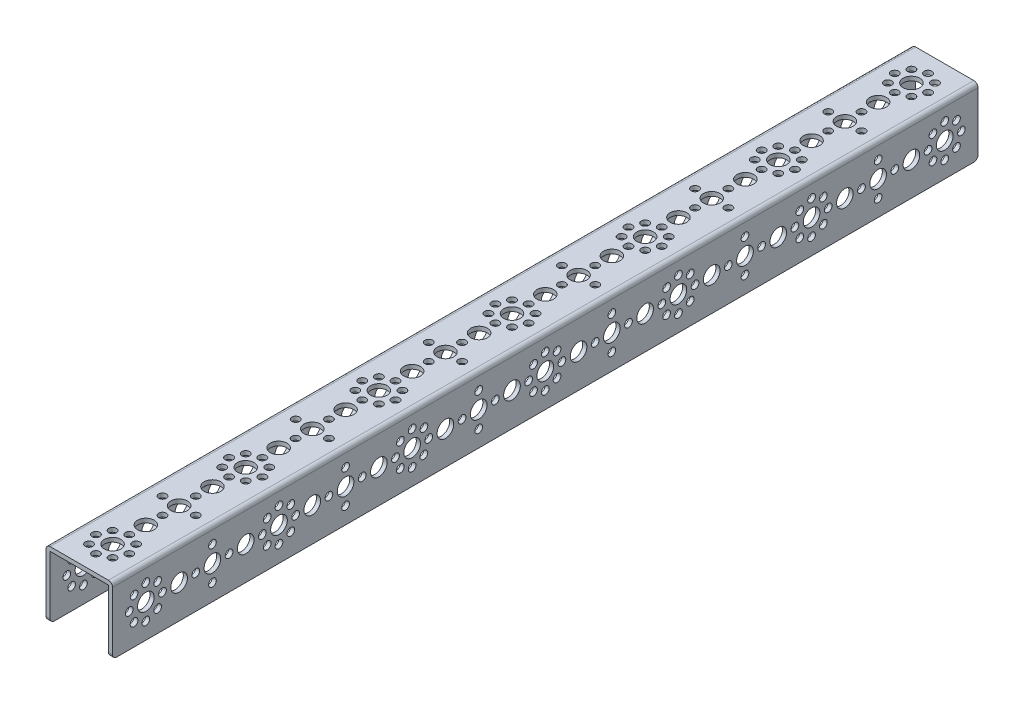
SolidWorks part; units mm, degrees
ref_plane "Front Plane" through (0, 0, 0) normal (0, 0, 1) x (1, 0, 0)
ref_plane "Top Plane" through (0, 0, 0) normal (0, 1, 0) x (1, 0, 0)
ref_plane "Right Plane" through (0, 0, 0) normal (1, 0, 0) x (0, 0, -1)
sketch "Sketch1" plane through (0, 0, 0) normal (0, 0, 1) x (1, 0, 0)
  line L0 (14, -16) -> (16, -16)
  line L1 (-16, 16) -> (16, 16)
  line L2 (-16, 16) -> (-16, -16)
  line L3 (-16, -16) -> (-14, -16)
  line L4 (16, 16) -> (16, -16)
  line L5 (-16, 16) -> (16, -16) construction
  line L6 (-16, -16) -> (16, 16) construction
  line L7 (-14, 14) -> (14, 14)
  line L8 (-14, 14) -> (-14, -16)
  line L10 (14, 14) -> (14, -16)
  point P0 (0, 0)
  dimension "D1" = 32
  dimension "D2" = 32
  dimension "D3" = 2
  dimension "D4" = 2
extrude "Boss-Extrude1" add sketch "Sketch1" against normal blind 416
sketch "Sketch2" plane through (0, 16, 0) normal (0, 1, 0) x (1, 0, 0)
  line L0 (0, 0) -> (0, 307.3895) construction
  line L1 (16, 0) -> (-16, 0) construction
  line L2 (-28.6598, 208) -> (46.6801, 208) construction
  circle B0 centre (0, 256) radius 4
  circle B1 centre (0, 224) radius 4
  circle B2 centre (0.1754, 192) radius 4
  circle B3 centre (0, 160) radius 4
  circle B4 centre (0, 240) radius 4
  circle B5 centre (0, 232) radius 1.85
  circle B6 centre (0, 248) radius 1.85
  circle B7 centre (-8, 240) radius 1.85
  circle B8 centre (8, 240) radius 1.85
  circle B9 centre (0, 264) radius 1.85
  circle B10 centre (-8, 272) radius 1.85
  circle B11 centre (0, 272) radius 4
  circle B12 centre (8, 272) radius 1.85
  circle B13 centre (5.66, 277.66) radius 1.85
  circle B14 centre (-5.66, 277.66) radius 1.85
  circle B15 centre (0, 280) radius 1.85
  circle B16 centre (5.66, 266.34) radius 1.85
  circle B17 centre (-5.66, 266.34) radius 1.85
  circle B18 centre (0, 176) radius 4
  circle B19 centre (0, 168) radius 1.85
  circle B20 centre (0, 184) radius 1.85
  circle B21 centre (-8, 176) radius 1.85
  circle B22 centre (8, 176) radius 1.85
  circle B23 centre (0, 200) radius 1.85
  circle B24 centre (-8, 208) radius 1.85
  circle B25 centre (0, 208) radius 4
  circle B26 centre (8, 208) radius 1.85
  circle B27 centre (5.66, 213.66) radius 1.85
  circle B28 centre (-5.66, 213.66) radius 1.85
  circle B29 centre (0, 216) radius 1.85
  circle B30 centre (5.66, 202.34) radius 1.85
  circle B31 centre (-5.66, 202.34) radius 1.85
  circle B32 centre (0, 32) radius 4
  circle B33 centre (0, 64) radius 4
  circle B34 centre (-0.1754, 96) radius 4
  circle B35 centre (0, 128) radius 4
  circle B36 centre (0, 48) radius 4
  circle B37 centre (0, 56) radius 1.85
  circle B38 centre (0, 40) radius 1.85
  circle B39 centre (8, 48) radius 1.85
  circle B40 centre (-8, 48) radius 1.85
  circle B41 centre (0, 24) radius 1.85
  circle B42 centre (8, 16) radius 1.85
  circle B43 centre (0, 16) radius 4
  circle B44 centre (-8, 16) radius 1.85
  circle B45 centre (-5.66, 10.34) radius 1.85
  circle B46 centre (5.66, 10.34) radius 1.85
  circle B47 centre (0, 8) radius 1.85
  circle B48 centre (-5.66, 21.66) radius 1.85
  circle B49 centre (5.66, 21.66) radius 1.85
  circle B50 centre (0, 112) radius 4
  circle B51 centre (0, 120) radius 1.85
  circle B52 centre (0, 104) radius 1.85
  circle B53 centre (8, 112) radius 1.85
  circle B54 centre (-8, 112) radius 1.85
  circle B55 centre (0, 88) radius 1.85
  circle B56 centre (8, 80) radius 1.85
  circle B57 centre (0, 80) radius 4
  circle B58 centre (-8, 80) radius 1.85
  circle B59 centre (-5.66, 74.34) radius 1.85
  circle B60 centre (5.66, 74.34) radius 1.85
  circle B61 centre (0, 72) radius 1.85
  circle B62 centre (-5.66, 85.66) radius 1.85
  circle B63 centre (5.66, 85.66) radius 1.85
  circle B64 centre (0, 136) radius 1.85
  circle B65 centre (-8, 144) radius 1.85
  circle B66 centre (0, 144) radius 4
  circle B67 centre (8, 144) radius 1.85
  circle B68 centre (5.66, 149.66) radius 1.85
  circle B69 centre (-5.66, 149.66) radius 1.85
  circle B70 centre (0, 152) radius 1.85
  circle B71 centre (5.66, 138.34) radius 1.85
  circle B72 centre (-5.66, 138.34) radius 1.85
  circle B73 centre (0, 384) radius 4
  circle B74 centre (0, 352) radius 4
  circle B75 centre (0.1754, 320) radius 4
  circle B76 centre (0, 288) radius 4
  circle B77 centre (0, 368) radius 4
  circle B78 centre (0, 360) radius 1.85
  circle B79 centre (0, 376) radius 1.85
  circle B80 centre (-8, 368) radius 1.85
  circle B81 centre (8, 368) radius 1.85
  circle B82 centre (0, 392) radius 1.85
  circle B83 centre (-8, 400) radius 1.85
  circle B84 centre (0, 400) radius 4
  circle B85 centre (8, 400) radius 1.85
  circle B86 centre (5.66, 405.66) radius 1.85
  circle B87 centre (-5.66, 405.66) radius 1.85
  circle B88 centre (0, 408) radius 1.85
  circle B89 centre (5.66, 394.34) radius 1.85
  circle B90 centre (-5.66, 394.34) radius 1.85
  circle B91 centre (0, 304) radius 4
  circle B92 centre (0, 296) radius 1.85
  circle B93 centre (0, 312) radius 1.85
  circle B94 centre (-8, 304) radius 1.85
  circle B95 centre (8, 304) radius 1.85
  circle B96 centre (0, 328) radius 1.85
  circle B97 centre (-8, 336) radius 1.85
  circle B98 centre (0, 336) radius 4
  circle B99 centre (8, 336) radius 1.85
  circle B100 centre (5.66, 341.66) radius 1.85
  circle B101 centre (-5.66, 341.66) radius 1.85
  circle B102 centre (0, 344) radius 1.85
  circle B103 centre (5.66, 330.34) radius 1.85
  circle B104 centre (-5.66, 330.34) radius 1.85
sketch_block_instance "TETRIX 416 Pattern-1"
sketch_block "TETRIX 416 Pattern"
extrude "Cut-Extrude1" cut sketch "Sketch2" against normal through all
sketch "Sketch3" plane through (16, 0, 0) normal (1, 0, 0) x (0, 0, -1)
  line L0 (0, 0) -> (266.4146, 0) construction
  line L1 (208, 26.2638) -> (208, -32.4653) construction
  circle B0 centre (160, 0) radius 4
  circle B1 centre (192, 0) radius 4
  circle B2 centre (224, 0.1754) radius 4
  circle B3 centre (256, 0) radius 4
  circle B4 centre (176, 0) radius 4
  circle B5 centre (184, 0) radius 1.85
  circle B6 centre (168, 0) radius 1.85
  circle B7 centre (176, -8) radius 1.85
  circle B8 centre (176, 8) radius 1.85
  circle B9 centre (152, 0) radius 1.85
  circle B10 centre (144, -8) radius 1.85
  circle B11 centre (144, 0) radius 4
  circle B12 centre (144, 8) radius 1.85
  circle B13 centre (138.34, 5.66) radius 1.85
  circle B14 centre (138.34, -5.66) radius 1.85
  circle B15 centre (136, 0) radius 1.85
  circle B16 centre (149.66, 5.66) radius 1.85
  circle B17 centre (149.66, -5.66) radius 1.85
  circle B18 centre (240, 0) radius 4
  circle B19 centre (248, 0) radius 1.85
  circle B20 centre (232, 0) radius 1.85
  circle B21 centre (240, -8) radius 1.85
  circle B22 centre (240, 8) radius 1.85
  circle B23 centre (216, 0) radius 1.85
  circle B24 centre (208, -8) radius 1.85
  circle B25 centre (208, 0) radius 4
  circle B26 centre (208, 8) radius 1.85
  circle B27 centre (202.34, 5.66) radius 1.85
  circle B28 centre (202.34, -5.66) radius 1.85
  circle B29 centre (200, 0) radius 1.85
  circle B30 centre (213.66, 5.66) radius 1.85
  circle B31 centre (213.66, -5.66) radius 1.85
  circle B32 centre (384, 0) radius 4
  circle B33 centre (352, 0) radius 4
  circle B34 centre (320, -0.1754) radius 4
  circle B35 centre (288, 0) radius 4
  circle B36 centre (368, 0) radius 4
  circle B37 centre (360, 0) radius 1.85
  circle B38 centre (376, 0) radius 1.85
  circle B39 centre (368, 8) radius 1.85
  circle B40 centre (368, -8) radius 1.85
  circle B41 centre (392, 0) radius 1.85
  circle B42 centre (400, 8) radius 1.85
  circle B43 centre (400, 0) radius 4
  circle B44 centre (400, -8) radius 1.85
  circle B45 centre (405.66, -5.66) radius 1.85
  circle B46 centre (405.66, 5.66) radius 1.85
  circle B47 centre (408, 0) radius 1.85
  circle B48 centre (394.34, -5.66) radius 1.85
  circle B49 centre (394.34, 5.66) radius 1.85
  circle B50 centre (304, 0) radius 4
  circle B51 centre (296, 0) radius 1.85
  circle B52 centre (312, 0) radius 1.85
  circle B53 centre (304, 8) radius 1.85
  circle B54 centre (304, -8) radius 1.85
  circle B55 centre (328, 0) radius 1.85
  circle B56 centre (336, 8) radius 1.85
  circle B57 centre (336, 0) radius 4
  circle B58 centre (336, -8) radius 1.85
  circle B59 centre (341.66, -5.66) radius 1.85
  circle B60 centre (341.66, 5.66) radius 1.85
  circle B61 centre (344, 0) radius 1.85
  circle B62 centre (330.34, -5.66) radius 1.85
  circle B63 centre (330.34, 5.66) radius 1.85
  circle B64 centre (280, 0) radius 1.85
  circle B65 centre (272, -8) radius 1.85
  circle B66 centre (272, 0) radius 4
  circle B67 centre (272, 8) radius 1.85
  circle B68 centre (266.34, 5.66) radius 1.85
  circle B69 centre (266.34, -5.66) radius 1.85
  circle B70 centre (264, 0) radius 1.85
  circle B71 centre (277.66, 5.66) radius 1.85
  circle B72 centre (277.66, -5.66) radius 1.85
  circle B73 centre (32, 0) radius 4
  circle B74 centre (64, 0) radius 4
  circle B75 centre (96, 0.1754) radius 4
  circle B76 centre (128, 0) radius 4
  circle B77 centre (48, 0) radius 4
  circle B78 centre (56, 0) radius 1.85
  circle B79 centre (40, 0) radius 1.85
  circle B80 centre (48, -8) radius 1.85
  circle B81 centre (48, 8) radius 1.85
  circle B82 centre (24, 0) radius 1.85
  circle B83 centre (16, -8) radius 1.85
  circle B84 centre (16, 0) radius 4
  circle B85 centre (16, 8) radius 1.85
  circle B86 centre (10.34, 5.66) radius 1.85
  circle B87 centre (10.34, -5.66) radius 1.85
  circle B88 centre (8, 0) radius 1.85
  circle B89 centre (21.66, 5.66) radius 1.85
  circle B90 centre (21.66, -5.66) radius 1.85
  circle B91 centre (112, 0) radius 4
  circle B92 centre (120, 0) radius 1.85
  circle B93 centre (104, 0) radius 1.85
  circle B94 centre (112, -8) radius 1.85
  circle B95 centre (112, 8) radius 1.85
  circle B96 centre (88, 0) radius 1.85
  circle B97 centre (80, -8) radius 1.85
  circle B98 centre (80, 0) radius 4
  circle B99 centre (80, 8) radius 1.85
  circle B100 centre (74.34, 5.66) radius 1.85
  circle B101 centre (74.34, -5.66) radius 1.85
  circle B102 centre (72, 0) radius 1.85
  circle B103 centre (85.66, 5.66) radius 1.85
  circle B104 centre (85.66, -5.66) radius 1.85
sketch_block_instance "TETRIX 416 Pattern-3"
extrude "Cut-Extrude2" cut sketch "Sketch3" against normal through all
fillet "Fillet1" radius 2 6 edges at (-15, -16, -416) (15, -16, -416) (-15, -16, 0) (15, -16, 0) (-16, 16, -208) (16, 16, -208)
